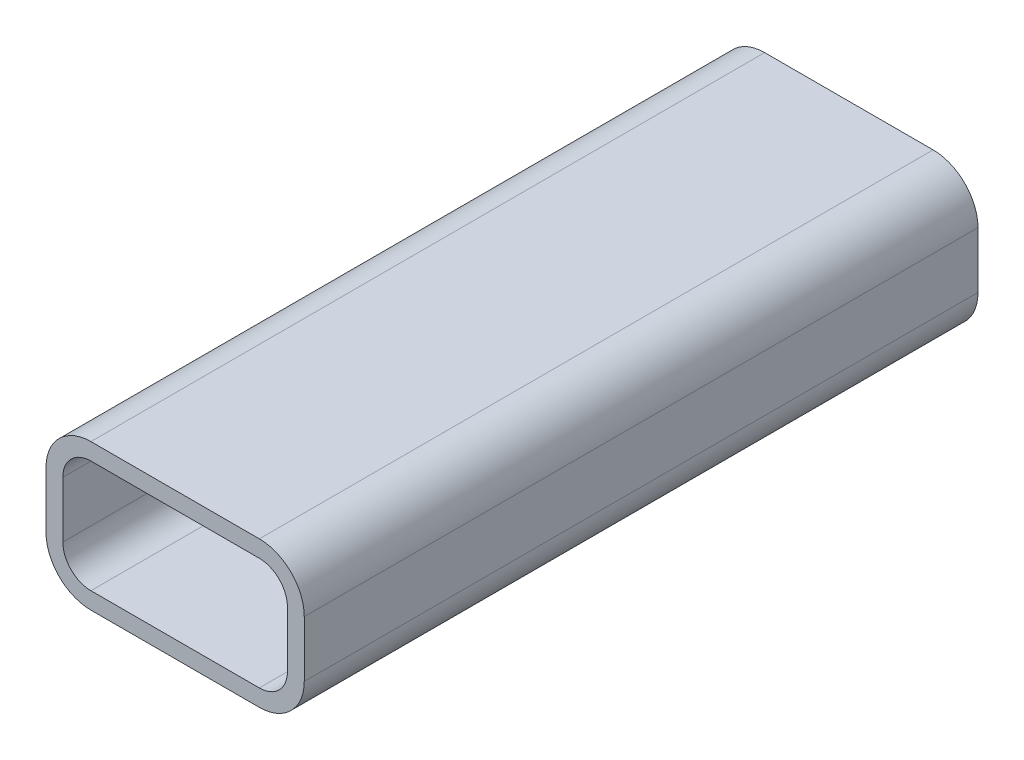
SolidWorks part; units mm, degrees
ref_plane "Front Plane" through (0, 0, 0) normal (0, 0, 1) x (1, 0, 0)
ref_plane "Top Plane" through (0, 0, 0) normal (0, 1, 0) x (1, 0, 0)
ref_plane "Right Plane" through (0, 0, 0) normal (1, 0, 0) x (0, 0, -1)
sketch "Sketch1" plane through (0, 0, 0) normal (0, 0, 1) x (1, 0, 0)
  line L1 (-15, 10) -> (15, 10)
  line L2 (-20, 5) -> (-20, -5)
  line L3 (-15, -10) -> (15, -10)
  line L4 (20, 5) -> (20, -5)
  line L5 (-20, 10) -> (20, -10) construction
  line L6 (-20, -10) -> (20, 10) construction
  arc A0 (15, 10) -> (20, 5) centre (15, 5) cw
  arc A1 (20, -5) -> (15, -10) centre (15, -5) cw
  arc A2 (-15, -10) -> (-20, -5) centre (-15, -5) cw
  arc A3 (-20, 5) -> (-15, 10) centre (-15, 5) cw
  point P0 (0, 0)
  dimension "D3" = 5
  dimension "D1" = 40
  dimension "D2" = 20
extrude "Extrude-Thin1" add sketch "Sketch1" along normal mid plane 120 thin thin type one direction wall 3
sketch "Sketch2" plane through (0, 13, 0) normal (0, 1, 0) x (1, 0, 0)
  line L0 (0, -45) -> (0, 45) construction
  line L1 (-6, -45) -> (-6, 45)
  line L2 (6, -45) -> (6, 45)
  arc A0 (-6, -45) -> (6, -45) centre (0, -45) ccw
  arc A1 (6, 45) -> (-6, 45) centre (0, 45) ccw
  point P2 (0, 0)
  dimension "D2" = 6
  dimension "D1" = 90
extrude "Cut-Extrude1" [suppressed] cut sketch "Sketch2" against normal through all
